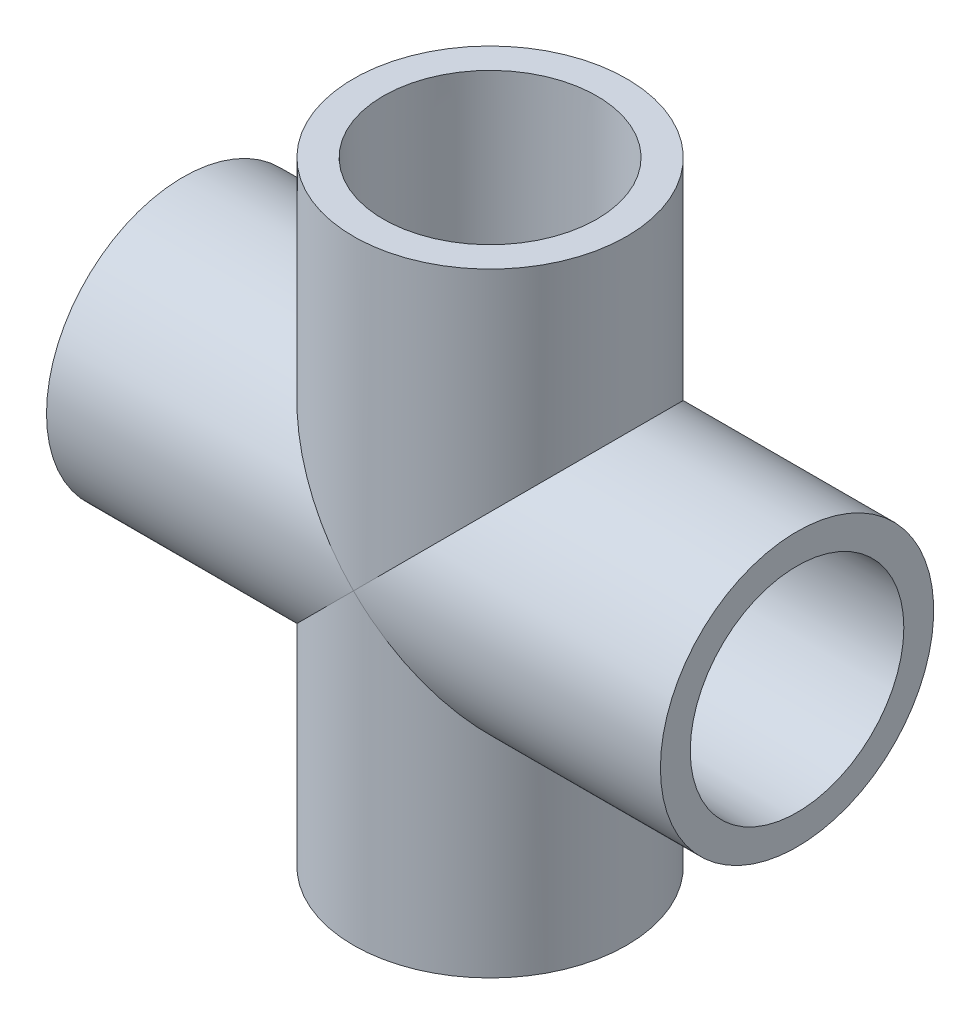
SolidWorks part; units mm, degrees
ref_plane "Front Plane" through (0, 0, 0) normal (0, 0, 1) x (1, 0, 0)
ref_plane "Top Plane" through (0, 0, 0) normal (0, 1, 0) x (1, 0, 0)
ref_plane "Right Plane" through (0, 0, 0) normal (1, 0, 0) x (0, 0, -1)
sketch "Sketch0" plane through (0, 0, 0) normal (0, 0, 1) x (1, 0, 0)
  line L0 (-30.9562, 0) -> (0, 0) construction
  line L1 (0, 0) -> (0, 30.9562) construction
  line L2 (-13.4937, 0) -> (0, 0) construction
  line L3 (0, 0) -> (0, 13.4937) construction
  line L4 (-30.9562, 13.7795) -> (-30.9562, -13.7795) construction
  line L5 (-13.4937, 10.6172) -> (-30.9562, 10.7696) construction
  line L6 (-13.4937, 10.6172) -> (-13.4937, -10.6172) construction
  line L7 (-13.4937, -10.6172) -> (-30.9562, -10.7696) construction
  line L8 (-30.9562, 10.7696) -> (-30.9562, -10.7696) construction
  line L9 (-13.7795, 30.9562) -> (13.7795, 30.9563) construction
  line L10 (-10.7696, 30.9562) -> (10.7696, 30.9563) construction
  line L11 (10.7696, 30.9563) -> (10.6172, 13.4937) construction
  line L12 (10.6172, 13.4937) -> (-10.6172, 13.4937) construction
  line L13 (-10.6172, 13.4937) -> (-10.7696, 30.9562) construction
  line L14 (-13.4937, 7.8994) -> (-13.4937, -7.8994) construction
  line L15 (-30.9562, 0) -> (-13.4937, 0) construction
  line L16 (0, 30.9562) -> (0, 13.4937) construction
  line L17 (0, 0) -> (13.4937, 0) construction
  line L18 (-7.8994, 13.4937) -> (7.8994, 13.4937) construction
  line L19 (13.4937, 0) -> (30.9562, 0) construction
  line L20 (0, 0) -> (0, -13.4937) construction
  line L21 (0, -13.4937) -> (0, -30.9562) construction
  dimension "H" = 30.9562
  dimension "G" = 13.4937
  dimension "M" = 27.559
  dimension "OD A" = 21.5392
  dimension "OD B" = 21.2344
  dimension "ID" = 15.7988
sketch "Sketch1" plane through (0, 0, 0) normal (0, 0, 1) x (1, 0, 0)
  line L0 (-30.9562, 0) -> (0, 0) construction
  line L1 (-30.9562, 0) -> (0, 0) construction
  line L2 (0, 0) -> (0, -13.7795) construction
  line L3 (-30.9562, -13.7795) -> (-13.4937, -13.7795)
  line L4 (-30.9562, -13.7795) -> (-30.9562, -10.7696)
  line L5 (-30.9562, -10.7696) -> (-13.4937, -10.6172)
  line L6 (-13.4937, -13.7795) -> (-13.4937, -10.6172)
  line L7 (-13.4937, -13.7795) -> (0, -13.7795) construction
  line L8 (30.9562, -10.7696) -> (13.4937, -10.6172)
  line L9 (30.9562, -13.7795) -> (30.9562, -10.7696)
  line L10 (13.4937, -13.7795) -> (13.4937, -10.6172)
  line L11 (30.9562, -13.7795) -> (13.4937, -13.7795)
revolve "Revolve1" add sketch "Sketch1" angle 360 about L1
sketch "Sketch2" plane through (0, 0, 0) normal (0, 0, 1) x (1, 0, 0)
  line L0 (10.7696, 30.9563) -> (10.6172, 13.4937)
  line L1 (10.6172, 13.4937) -> (13.7795, 13.4937)
  line L2 (13.7795, 13.4937) -> (13.7795, 30.9563)
  line L3 (13.7795, 30.9563) -> (10.7696, 30.9563)
  line L4 (0, 0) -> (0, 30.9562) construction
  line L5 (0, 0) -> (0, 30.9562) construction
  line L6 (0, 0) -> (13.4937, 0) construction
  line L7 (13.7795, -30.9563) -> (10.7696, -30.9563)
  line L8 (13.7795, -13.4937) -> (13.7795, -30.9563)
  line L9 (10.6172, -13.4937) -> (13.7795, -13.4937)
  line L10 (10.7696, -30.9563) -> (10.6172, -13.4937)
revolve "Revolve2" add sketch "Sketch2" angle 360 about L5
sketch "Sketch3" plane through (-13.4937, 0, 0) normal (1, 0, 0) x (0, 0, -1)
  circle A0 centre (0, 0) radius 7.8994
  circle A1 centre (0, 0) radius 13.7795
sketch "Sketch4" plane through (-13.4937, 0, 0) normal (1, 0, 0) x (0, 0, -1)
  circle A0 centre (0, 0) radius 13.7795 construction
  circle A1 centre (0, 0) radius 13.7795
extrude "Boss-Extrude1" add sketch "Sketch4" along normal up to vertex
sketch "Sketch5" plane through (0, 13.4938, 0) normal (0, -1, 0) x (1, 0, 0)
  circle A0 centre (0, 0) radius 13.7795 construction
  circle A1 centre (0, 0) radius 13.7795
extrude "Boss-Extrude2" add sketch "Sketch5" along normal up to vertex
sketch "Sketch6" plane through (0, 0, 0) normal (0, 0, 1) x (1, 0, 0)
  line L0 (-30.9562, -10.7696) -> (-13.4937, -10.6172)
  line L1 (-13.4937, -10.6172) -> (-13.4937, -7.8994)
  line L2 (-13.4937, -7.8994) -> (13.4937, -7.8994)
  line L3 (13.4937, -10.2436) -> (13.4937, 10.2436) construction
  line L4 (0, -7.8994) -> (0, 0) construction
  line L5 (13.4937, -10.6172) -> (13.4937, -7.8994)
  line L6 (30.9562, -10.7696) -> (30.9562, 10.7696) construction
  line L7 (30.9562, -13.7795) -> (30.9562, 13.7795) construction
  line L8 (30.9562, -10.7696) -> (30.9563, 0)
  line L9 (30.9563, 0) -> (-30.9562, 0)
  line L10 (-30.9562, 0) -> (-30.9562, -10.7696)
  line L11 (30.9562, -10.7696) -> (13.4937, -10.6172)
revolve "Cut-Revolve1" cut sketch "Sketch6" angle 360 about L9
sketch "Sketch7" plane through (0, 0, 0) normal (0, 0, 1) x (1, 0, 0)
  line L0 (10.7696, 30.9563) -> (10.6172, 13.4937)
  line L1 (10.6172, 13.4937) -> (7.8994, 13.4937)
  line L2 (7.8994, 13.4937) -> (7.8994, -13.4938)
  line L4 (7.8994, 0) -> (0, 0) construction
  line L5 (0, 30.9562) -> (0, -30.9562)
  line L6 (-13.7795, 30.9562) -> (13.7795, 30.9563) construction
  line L7 (0, 30.9562) -> (10.7696, 30.9563)
  line L8 (10.6172, -13.4938) -> (7.8994, -13.4938)
  line L9 (10.7696, -30.9563) -> (10.6172, -13.4938)
  line L10 (0, 0) -> (13.4937, 0) construction
  line L11 (0, -30.9562) -> (10.7696, -30.9563)
revolve "Cut-Revolve2" cut sketch "Sketch7" angle 360 about L5
